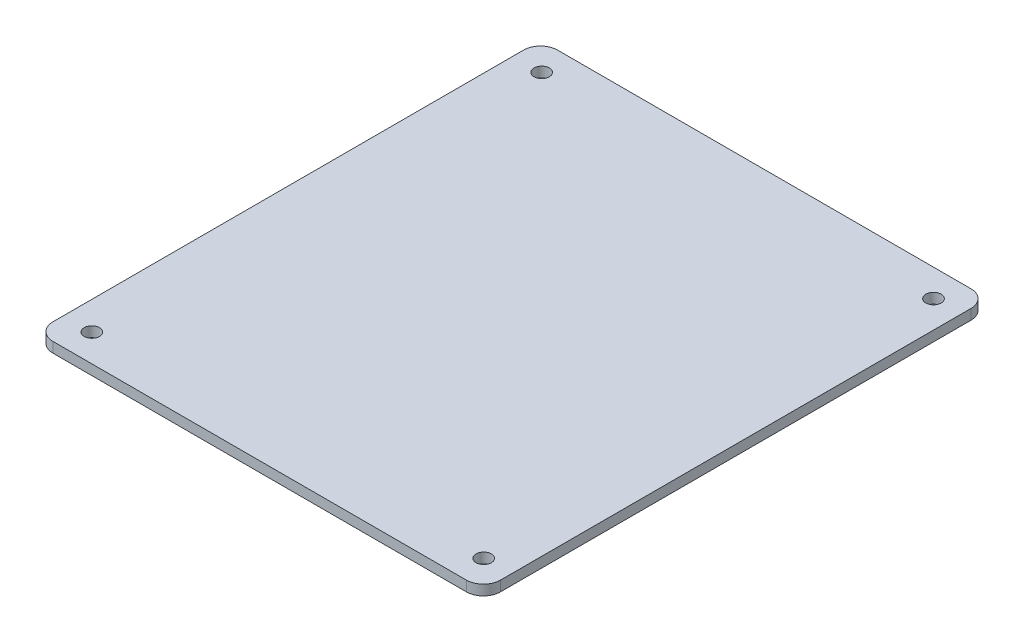
SolidWorks part; units mm, degrees
ref_plane "Front Plane" through (0, 0, 0) normal (0, 0, 1) x (1, 0, 0)
ref_plane "Top Plane" through (0, 0, 0) normal (0, 1, 0) x (1, 0, 0)
ref_plane "Right Plane" through (0, 0, 0) normal (1, 0, 0) x (0, 0, -1)
sketch "Sketch1" plane through (0, 0, 0) normal (0, 1, 0) x (1, 0, 0)
  line L0 (66.0659, -73.8375) -> (66.0659, 74.2445) construction
  line L5 (-65.2521, -73.8375) -> (66.0659, -73.8375) construction
  line L6 (-65.2521, 74.2445) -> (-65.2521, -73.8375) construction
  line L7 (66.0659, 74.2445) -> (-65.2521, 74.2445) construction
  line L8 (66.0659, -73.8375) -> (66.0659, 74.2445)
  line L9 (-65.2521, -73.8375) -> (66.0659, -73.8375)
  line L10 (-65.2521, 74.2445) -> (-65.2521, -73.8375)
  line L11 (66.0659, 74.2445) -> (-65.2521, 74.2445)
extrude "Boss-Extrude1" add sketch "Sketch1" along normal blind 3
sketch "Sketch2" plane through (0, 3, 0) normal (0, 1, 0) x (1, 0, 0)
  circle A0 centre (-56.9341, -65.7555) radius 2.25
  circle A1 centre (-56.9341, 66.2445) radius 2.25
  circle A2 centre (58.0659, 66.2445) radius 2.25
  circle A3 centre (58.0659, -65.7555) radius 2.25
extrude "Cut-Extrude1" cut sketch "Sketch2" against normal through all
fillet "Fillet1" radius 5 4 edges at (-65.2521, 1.5, -74.2445) (66.0659, 1.5, -74.2445) (-65.2521, 1.5, 73.8375) (66.0659, 1.5, 73.8375)
